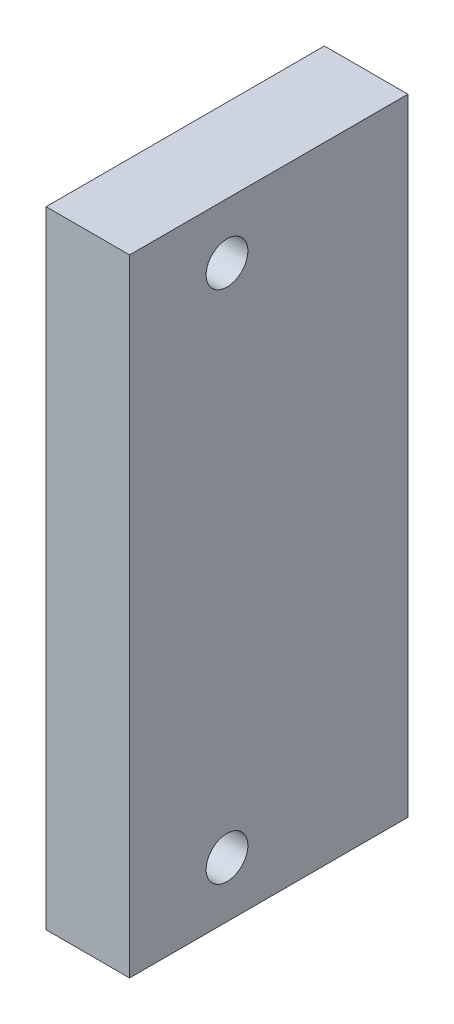
SolidWorks part; units mm, degrees
ref_plane "Front" through (0, 0, 0) normal (0, 0, 1) x (1, 0, 0)
ref_plane "Top" through (0, 0, 0) normal (0, 1, 0) x (1, 0, 0)
ref_plane "Right" through (0, 0, 0) normal (1, 0, 0) x (0, 0, -1)
sketch "Sketch1" plane through (0, 0, 0) normal (0, 0, 1) x (1, 0, 0)
  line L0 (0, 0) -> (-11.4466, 0) construction
  line L2 (-13, 22.5) -> (-7, 22.5)
  line L3 (-13, 22.5) -> (-13, -22.5)
  line L4 (-13, -22.5) -> (-7, -22.5)
  line L5 (-7, 22.5) -> (-7, -22.5)
  line L6 (-13, 22.5) -> (-7, -22.5) construction
  line L7 (-13, -22.5) -> (-7, 22.5) construction
  point P1 (-10, 0)
  dimension "D1" = 10
  dimension "D2" = 45
  dimension "D3" = 6
extrude "Boss-Extrude1" add sketch "Sketch1" along normal blind 20 contours L3 L4 L5 L2
sketch "Sketch2" plane through (-13, 0, 0) normal (-1, 0, 0) x (0, 0, 1)
  line L0 (0, 0) -> (50000, 0) construction
  line L1 (0, 22.5) -> (0, -22.5) construction
  line L2 (20, 22.5) -> (20, -22.5) construction
  line L3 (13, 0) -> (13, -22.5) construction
  line L4 (20, -22.5) -> (0, -22.5) construction
  circle A0 centre (13, -18.5) radius 1.5
  circle A1 centre (13, 18.5) radius 1.5
  point P4 (0, 0)
  point P7 (20, 0)
  dimension "D1" = 3
  dimension "D2" = 37
  dimension "D3" = 7
extrude "Cut-Extrude2" cut sketch "Sketch2" against normal through all contours A0 | A1
